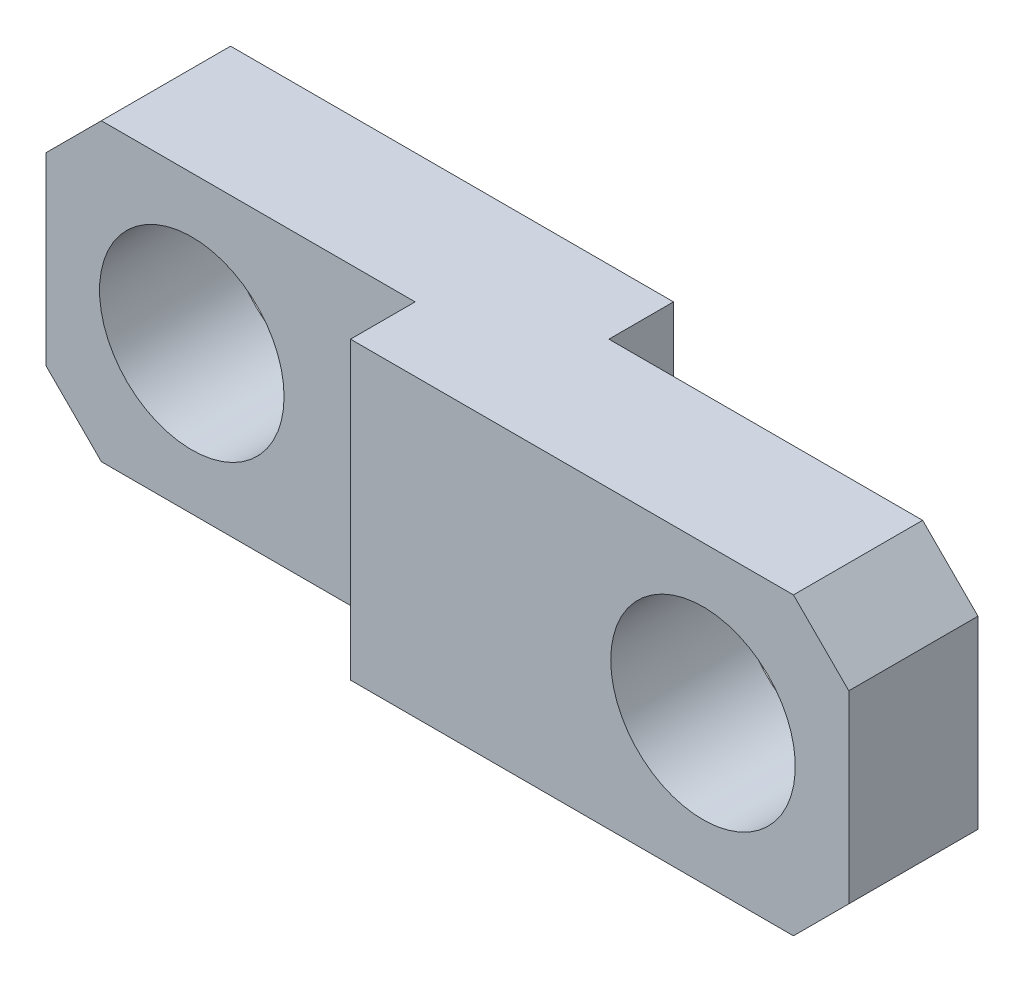
SolidWorks part; units mm, degrees
ref_plane "Face" through (0, 0, 0) normal (0, 0, 1) x (1, 0, 0)
ref_plane "Dessus" through (0, 0, 0) normal (0, 1, 0) x (1, 0, 0)
ref_plane "Droite" through (0, 0, 0) normal (1, 0, 0) x (0, 0, -1)
sketch "Esquisse1" plane through (0, 0, 0) normal (0, 0, 1) x (1, 0, 0)
  line L0 (-8, 0) -> (25, 0) construction
  line L1 (-3.95, 4) -> (19.55, 4)
  line L2 (-3.95, -4) -> (19.55, -4)
  line L3 (7.8, 8) -> (7.8, -9) construction
  line L4 (-3.95, 4) -> (-3.95, -4)
  line L5 (19.55, 4) -> (19.55, -4)
  circle A0 centre (0, 0) radius 2.5
  circle A1 centre (15.6, 0) radius 2.5
  point P10 (7.8, 4)
  point P15 (7.8, -4)
  dimension "D1" = 15.6
  dimension "D2" = 5
  dimension "D3" = 23.5
  dimension "D4" = 8
extrude "Base-Extrusion" add sketch "Esquisse1" along normal mid plane 5.25
sketch "Esquisse2" plane through (0, 0, 2.625) normal (0, 0, 1) x (1, 0, 0)
  line L0 (6.05, -4) -> (6.05, 4)
  line L1 (-3.95, -4) -> (19.55, -4) construction
  line L3 (19.55, 4) -> (-3.95, 4) construction
  line L4 (-3.95, 4) -> (-3.95, -4) construction
  line L9 (-3.95, 4) -> (-3.95, -4)
  line L10 (-3.95, -4) -> (19.55, -4)
  line L11 (19.55, -4) -> (19.55, 4)
  line L12 (19.55, 4) -> (-3.95, 4)
  line L13 (-3.95, 4) -> (-3.95, -4)
  line L14 (-3.95, -4) -> (6.05, -4)
  line L16 (6.05, 4) -> (-3.95, 4)
  dimension "D1" = 10
  dimension "D4" = 0
extrude "Enlèv. mat.-Extru.1" cut sketch "Esquisse2" against normal blind 1.75
sketch "Esquisse3" plane through (0, 0, -2.625) normal (0, 0, -1) x (-1, 0, 0)
  line L0 (-9.55, 4) -> (-9.55, -2)
  line L1 (-19.55, 4) -> (3.95, 4) construction
  line L2 (-9.55, -2) -> (-6.0859, -4)
  line L3 (3.95, -4) -> (-19.55, -4) construction
  line L4 (-19.55, -4) -> (-19.55, 4) construction
  line L9 (3.95, -4) -> (3.95, 4)
  line L10 (3.95, 4) -> (-19.55, 4)
  line L11 (-19.55, 4) -> (-19.55, -4)
  line L12 (-19.55, -4) -> (3.95, -4)
  line L14 (-9.55, 4) -> (-19.55, 4)
  line L15 (-19.55, 4) -> (-19.55, -4)
  line L16 (-19.55, -4) -> (-6.0859, -4)
  dimension "D1" = 10
  dimension "D2" = 2
  dimension "D3" = 30
  dimension "D4" = 0
extrude "Enlèv. mat.-Extru.2" cut sketch "Esquisse3" against normal blind 1.75
chamfer "Chanfrein1" distance 1.5 angle 45
